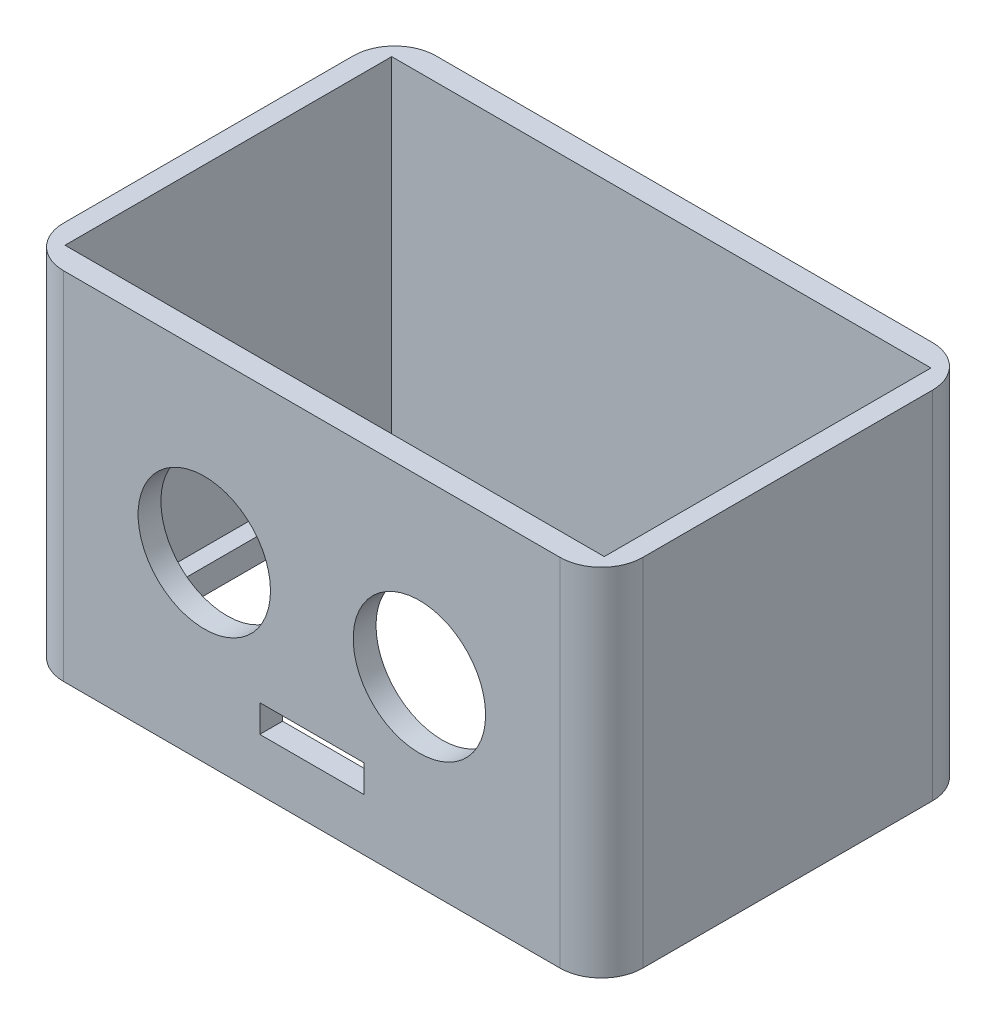
SolidWorks part; units mm, degrees
ref_plane "前视基准面" through (0, 0, 0) normal (0, 0, 1) x (1, 0, 0)
ref_plane "上视基准面" through (0, 0, 0) normal (0, 1, 0) x (1, 0, 0)
ref_plane "右视基准面" through (0, 0, 0) normal (1, 0, 0) x (0, 0, -1)
sketch "草图1" plane through (0, 0, 0) normal (0, 1, 0) x (1, 0, 0)
  line L1 (-35, 22.5) -> (35, 22.5)
  line L2 (-35, 22.5) -> (-35, -22.5)
  line L3 (-35, -22.5) -> (35, -22.5)
  line L4 (35, 22.5) -> (35, -22.5)
  line L5 (-35, 22.5) -> (35, -22.5) construction
  line L6 (-35, -22.5) -> (35, 22.5) construction
  point P0 (0, 0)
  dimension "D1" = 70
  dimension "D2" = 45
extrude "凸台-拉伸1" add sketch "草图1" along normal blind 3
ref_plane "基准面1" through (0, 3, 0) normal (0, 1, 0) x (1, 0, 0)
sketch "草图2" plane through (0, 3, 0) normal (0, 1, 0) x (1, 0, 0)
  line L0 (35, 22.5) -> (-35, 22.5) construction
  line L1 (17.5, 11.5) -> (30.5, 11.5)
  line L2 (17.5, 11.5) -> (17.5, -11.5)
  line L3 (17.5, -11.5) -> (30.5, -11.5)
  line L4 (30.5, 11.5) -> (30.5, -11.5)
  line L5 (35, -22.5) -> (35, 22.5) construction
  line L6 (-30.5, 11.5) -> (-17.5, 11.5)
  line L7 (-30.5, 11.5) -> (-30.5, -11.5)
  line L8 (-30.5, -11.5) -> (-17.5, -11.5)
  line L9 (-17.5, 11.5) -> (-17.5, -11.5)
  dimension "D1" = 23
  dimension "D2" = 13
  dimension "D3" = 11
  dimension "D4" = 11
  dimension "D5" = 23
  dimension "D6" = 13
  dimension "D7" = 35
  dimension "D8" = 4.5
extrude "切除-拉伸1" cut sketch "草图2" against normal blind 10
sketch "草图3" plane through (0, 3, 0) normal (0, 1, 0) x (1, 0, 0)
  line L0 (-24, 11.5) -> (-24, 14) construction
  line L1 (-17.5, 11.5) -> (-30.5, 11.5) construction
  line L2 (-24, -11.5) -> (-24, -14) construction
  line L3 (-30.5, -11.5) -> (-17.5, -11.5) construction
  line L4 (24, 11.5) -> (24, 14) construction
  line L5 (30.5, 11.5) -> (17.5, 11.5) construction
  line L6 (24, -11.5) -> (24, -14) construction
  line L7 (17.5, -11.5) -> (30.5, -11.5) construction
  circle A0 centre (-24, 14) radius 0.95
  circle A1 centre (-24, -14) radius 0.95
  circle A2 centre (24, 14) radius 0.95
  circle A3 centre (24, -14) radius 0.95
  dimension "D2" = 1.9
  dimension "D4" = 1.9
  dimension "D7" = 1.9
  dimension "D8" = 1.9
  dimension "D1" = 2.5
  dimension "D3" = 2.5
  dimension "D5" = 2.5
  dimension "D6" = 2.5
extrude "切除-拉伸2" cut sketch "草图3" against normal blind 10
fillet "圆角1" radius 5 1 edges at (35, 1.5, -22.5)
fillet "圆角2" radius 5 3 edges at (-35, 1.5, -22.5) (-35, 1.5, 22.5) (35, 1.5, 22.5)
sketch "草图4" plane through (0, 3, 0) normal (0, 1, 0) x (1, 0, 0)
  circle A0 centre (-30, 17.5) radius 0.95
  circle A1 centre (30, 17.5) radius 0.95
  circle A2 centre (-30, -17.5) radius 0.95
  circle A3 centre (30, -17.5) radius 0.95
  dimension "D1" = 1.9
  dimension "D2" = 1.9
  dimension "D3" = 1.9
  dimension "D4" = 1.9
extrude "切除-拉伸3" cut sketch "草图4" against normal blind 10
sketch "草图8" plane through (0, 3, 0) normal (0, 1, 0) x (1, 0, 0)
  line L0 (-27, 17.5) -> (27, 17.5)
  line L2 (30, 14.5) -> (30, -14.5)
  line L3 (-27, -17.5) -> (27, -17.5)
  line L4 (-30, 14.5) -> (-30, -14.5)
  arc A0 (-30, 14.5) -> (-27, 17.5) centre (-30, 17.5) ccw
  arc A1 (27, 17.5) -> (30, 14.5) centre (30, 17.5) ccw
  arc A2 (-27, -17.5) -> (-30, -14.5) centre (-30, -17.5) ccw
  arc A3 (30, -14.5) -> (27, -17.5) centre (30, -17.5) ccw
  dimension "D1" = 6
  dimension "D2" = 6
  dimension "D3" = 6
  dimension "D4" = 6
extrude "切除-拉伸4" cut sketch "草图8" against normal blind 10
sketch "草图9" plane through (0, 3, 0) normal (0, 1, 0) x (1, 0, 0)
  line L1 (-32.5913, 19.7445) -> (32.5913, 19.7445)
  line L2 (-32.5913, 19.7445) -> (-32.5913, -19.7445)
  line L3 (-32.5913, -19.7445) -> (32.5913, -19.7445)
  line L4 (32.5913, 19.7445) -> (32.5913, -19.7445)
  line L5 (-32.5913, 19.7445) -> (32.5913, -19.7445) construction
  line L6 (-32.5913, -19.7445) -> (32.5913, 19.7445) construction
  line L7 (-30, -22.5) -> (30, -22.5)
  line L8 (-35, -17.5) -> (-35, 17.5)
  line L9 (-30, 22.5) -> (30, 22.5)
  line L10 (35, -17.5) -> (35, 17.5)
  line L11 (-35, -22.5) -> (35, 22.5) construction
  line L12 (-35, 22.5) -> (35, -22.5) construction
  arc A0 (35, -17.5) -> (30, -22.5) centre (30, -17.5) cw
  arc A1 (-30, -22.5) -> (-35, -17.5) centre (-30, -17.5) cw
  arc A2 (35, 17.5) -> (30, 22.5) centre (30, 17.5) ccw
  arc A3 (-35, 17.5) -> (-30, 22.5) centre (-30, 17.5) cw
  point P0 (0, 0)
  point P6 (0, 0)
  point P23 (0, 0)
  dimension "D1" = 45
  dimension "D2" = 70
  dimension "D3" = 5
extrude "凸台-拉伸2" add sketch "草图9" along normal blind 40
ref_plane "基准面2" through (0, 0, 22.5) normal (0, 0, 1) x (1, 0, 0)
sketch "草图10" plane through (0, 0, 22.5) normal (0, 0, 1) x (1, 0, 0)
  line L0 (0, 0) -> (0, 22) construction
  line L1 (0, 22) -> (13, 22) construction
  line L2 (0, 22) -> (-13, 22) construction
  line L4 (-6.2936, 9.6489) -> (6.2936, 9.6489)
  line L5 (-6.2936, 9.6489) -> (-6.2936, 6.3248)
  line L6 (-6.2936, 6.3248) -> (6.2936, 6.3248)
  line L7 (6.2936, 9.6489) -> (6.2936, 6.3248)
  line L8 (-6.2936, 9.6489) -> (6.2936, 6.3248) construction
  line L9 (-6.2936, 6.3248) -> (6.2936, 9.6489) construction
  circle A0 centre (13, 22) radius 8
  circle A1 centre (-13, 22) radius 8
  point P7 (0, 7.9869)
  dimension "D1" = 16
  dimension "D2" = 16
  dimension "D3" = 26
  dimension "D4" = 13
  dimension "D5" = 22
extrude "切除-拉伸5" cut sketch "草图10" against normal blind 26
